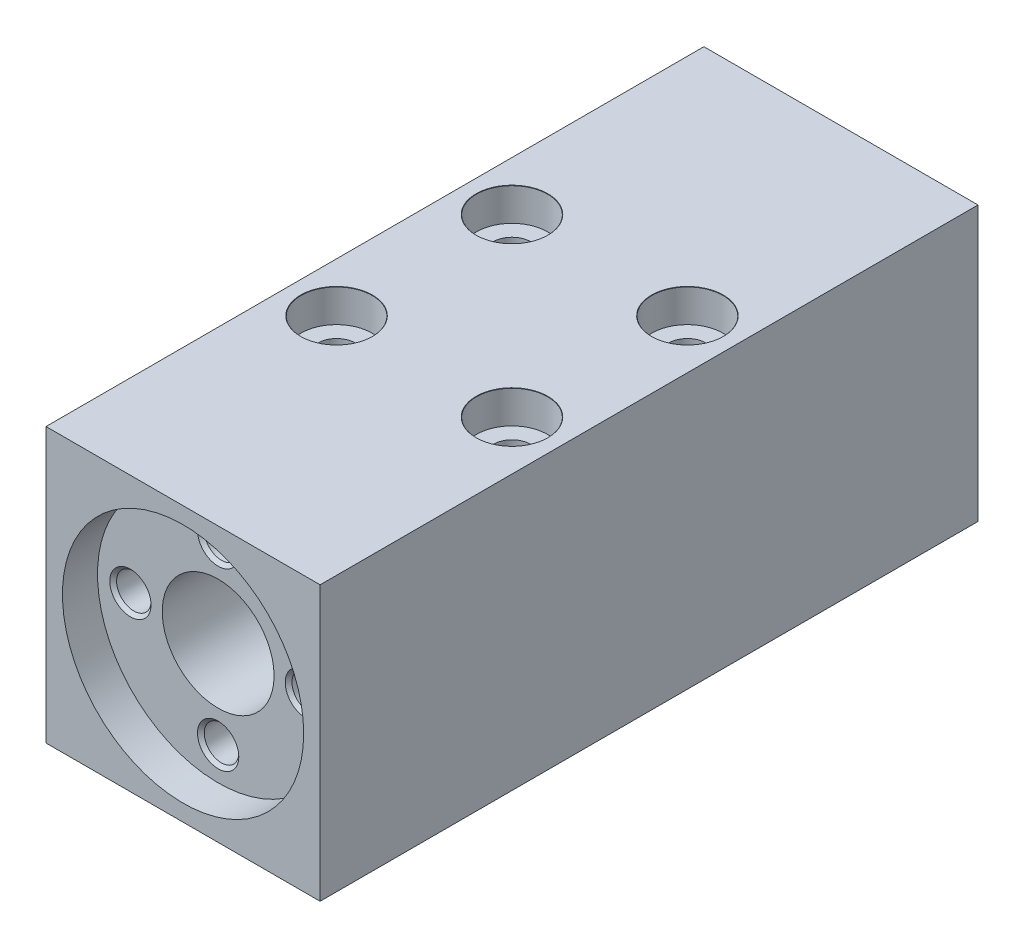
SolidWorks part; units mm, degrees
material "Liga 6061"
ref_plane "Plano frontal" through (0, 0, 0) normal (0, 0, 1) x (1, 0, 0)
ref_plane "Plano superior" through (0, 0, 0) normal (0, 1, 0) x (1, 0, 0)
ref_plane "Plano direito" through (0, 0, 0) normal (1, 0, 0) x (0, 0, -1)
sketch "Esboço1" plane through (0, 0, 0) normal (0, 0, 1) x (1, 0, 0)
  line L1 (12.5, -12.5) -> (-12.5, -12.5)
  line L2 (12.5, -12.5) -> (12.5, 12.5)
  line L3 (12.5, 12.5) -> (-12.5, 12.5)
  line L4 (-12.5, -12.5) -> (-12.5, 12.5)
  line L5 (12.5, -12.5) -> (-12.5, 12.5) construction
  line L6 (12.5, 12.5) -> (-12.5, -12.5) construction
  point P0 (0, 0)
  dimension "D1" = 25
  dimension "D2" = 25
extrude "Ressalto-extrusão1" add sketch "Esboço1" along normal blind 60
sketch "Esboço2" plane through (0, 0, 60) normal (0, 0, 1) x (1, 0, 0)
  line L0 (0, -13.6719) -> (0, 16.5889) construction
  circle A0 centre (0, 0) radius 5.1
  dimension "D1" = 10.2
extrude "Corte-extrusão1" cut sketch "Esboço2" against normal through all
sketch "Esboço3" plane through (0, 0, 60) normal (0, 0, 1) x (1, 0, 0)
  circle A0 centre (0, 0) radius 11
  dimension "D1" = 22
extrude "Corte-extrusão2" cut sketch "Esboço3" against normal blind 3.2
hole_wizard "Furo roscado para conduíte de M3x0.51" positions "Esboço4" profile "Esboço5" tap size "M3x0.5" standard "Helicoil® Metric"
sketch "Esboço4" plane through (0, 0, 56.8) normal (0, 0, 1) x (1, 0, 0)
  point P0 (0, 8)
  point P8 (8, 0)
  point P9 (0, -8)
  point P10 (-8, 0)
  dimension "D1" = 8
  dimension "D2" = 4
sketch "Esboço5" plane through (0, 8, 56.8) normal (1, 0, 0) x (0, -1, 0)
  line L0 (0, 0) -> (0, 6.9464)
  line L1 (0, 6.9464) -> (1.575, 6)
  line L2 (1.575, 6) -> (1.575, 0.308)
  line L3 (1.575, 0.308) -> (1.883, 0)
  line L5 (1.883, 0) -> (0, 0)
  line L6 (-1.575, 0.308) -> (-1.883, 0) construction
  line L10 (0, 6.9464) -> (-1.575, 6) construction
  line L11 (0, -6.35) -> (0, 107.95) construction
  dimension "Tap Drill Dia." = 3.15
  dimension "Tap Drill Depth" = 6
  dimension "Near C'Sink Dia." = 3.766
  dimension "Near C'Sink Angle" = 90
  dimension "Drill Angle" = 118
cosmetic thread "Rosca de furo1" parameters "D1"=3.5, "D2"=3.716
cosmetic thread "Rosca de furo2" parameters "D1"=3.5, "D2"=3.716
cosmetic thread "Rosca de furo3" parameters "D1"=3.5, "D2"=3.716
cosmetic thread "Rosca de furo4" parameters "D1"=3.5, "D2"=3.716
hole_wizard "Rebaixo para SHCS M31" positions "Esboço6" profile "Esboço7" counterbore size "M3" standard "Ansi Metric" end condition through all
sketch "Esboço6" plane through (0, 12.5, 0) normal (0, 1, 0) x (1, 0, 0)
  line L0 (0, 6.0284) -> (0, -65.2974) construction
  line L2 (13.0949, -30) -> (-19.5917, -30) construction
  point P0 (-8, -22)
  point P2 (8, -22)
  point P4 (-8, -38)
  point P6 (8, -38)
  dimension "D1" = 8
  dimension "D2" = 8
  dimension "D3" = 8
  dimension "D4" = 8
  dimension "D5" = 8
  dimension "D6" = 8
  dimension "D7" = 8
  dimension "D8" = 8
sketch "Esboço7" plane through (-8, 12.5, 22) normal (1, 0, 0) x (0, 0, 1)
  line L0 (0, 0) -> (0, 25)
  line L1 (0, 25) -> (1.7, 25)
  line L3 (1.7, 25) -> (1.7, 3)
  line L4 (3.25, 3) -> (1.7, 3)
  line L5 (3.25, 3) -> (3.25, 0.025)
  line L6 (3.25, 0.025) -> (3.275, 0)
  line L7 (3.275, 0) -> (0, 0)
  line L8 (-3.25, 0.025) -> (-3.275, 0) construction
  line L11 (0, -6.35) -> (0, 107.95) construction
  dimension "Thru Hole Dia." = 3.4
  dimension "Thru Hole Depth" = 25
  dimension "C'Bore Dia." = 6.5
  dimension "C'Bore Depth" = 3
  dimension "Near C'Sink Dia." = 6.55
  dimension "Near C'Sink Angle" = 90
